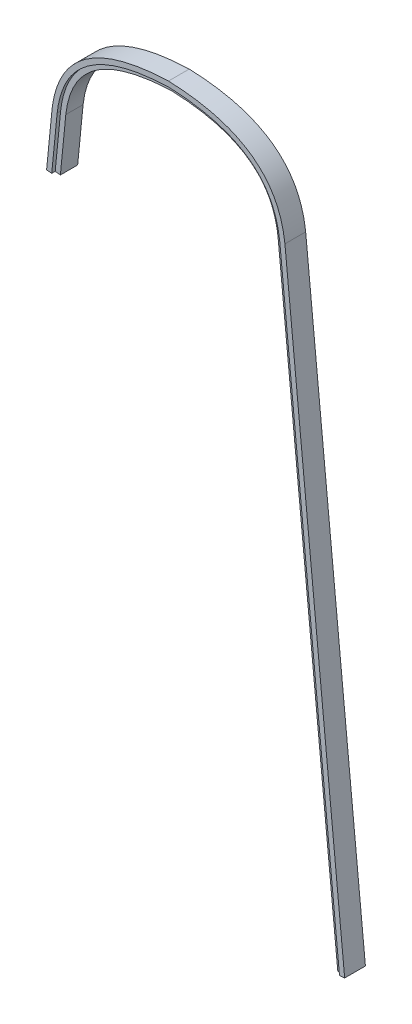
SolidWorks part; units mm, degrees
ref_plane "Front Plane" through (0, 0, 0) normal (0, 0, 1) x (1, 0, 0)
ref_plane "Top Plane" through (0, 0, 0) normal (0, 1, 0) x (1, 0, 0)
ref_plane "Right Plane" through (0, 0, 0) normal (1, 0, 0) x (0, 0, -1)
sketch "Sketch1" plane through (0, 0, 0) normal (0, 0, 1) x (1, 0, 0)
  line L0 (152.2242, 179.7953) -> (97.404, 735.8286)
  line L1 (-102.3813, 685.3442) -> (-97.404, 735.8286)
  line L2 (-111.8604, 686.2788) -> (-102.3813, 685.3442)
  line L3 (152.2242, 179.7953) -> (161.7032, 180.7299)
  line L4 (-166.6875, 130.175) -> (-106.8761, 736.8337) construction
  line L5 (-156.6942, 134.4562) -> (-97.404, 735.8286) construction
  line L6 (-111.8604, 686.2788) -> (-106.8761, 736.8337)
  line L7 (161.7032, 180.7299) -> (106.8761, 736.8337)
  line L8 (0, 0) -> (-166.6875, 130.175) construction
  line L9 (0, 12.0854) -> (-156.6942, 134.4562) construction
  line L10 (0, 0) -> (166.6875, 130.175) construction
  line L11 (0, 12.0854) -> (156.6942, 134.4562) construction
  line L12 (156.6942, 134.4562) -> (97.404, 735.8286) construction
  line L13 (166.6875, 130.175) -> (106.8761, 736.8337) construction
  spline S1 degree 2 poles (-106.8761, 736.8337) (-98.6556, 809.3851) (0, 812.8) knots 0 0 0 1 1 1
  spline S3 degree 2 poles (106.8761, 736.8337) (98.6556, 809.3851) (0, 812.8) knots 0 0 0 1 1 1
  spline S4 degree 1 poles (-97.404, 735.8286) (0, 803.2691) knots 0 0 1 1 construction
  spline S5 degree 1 poles (97.404, 735.8286) (0, 803.2691) knots 0 0 1 1 construction
  spline S8 degree 3 poles (-97.404, 735.8286) (-97.3262, 736.511) (-97.1554, 737.882) (-96.764, 740.5535) (-96.1774, 743.8053) (-95.3214, 747.555) (-93.9799, 752.3593) (-91.9331, 758.0032) (-88.8953, 764.2283) (-85.2743, 769.9432) (-79.6482, 776.9324) (-71.0508, 784.5724) (-60.1295, 790.8325) (-49.8978, 794.9673) (-41.467, 797.6141) (-32.2731, 799.7901) (-23.9758, 801.1984) (-16.9573, 802.076) (-11.5049, 802.6082) (-6.8004, 802.946) (-2.9501, 803.1519) (-0.9798, 803.2339) (0, 803.2691) knots 0.000508 0.000508 0.000508 0.000508 0.016098 0.031688 0.062868 0.094048 0.125228 0.187588 0.249948 0.312308 0.374668 0.499388 0.624108 0.686468 0.748828 0.811188 0.873548 0.904727 0.935907 0.967087 0.982677 0.998267 0.998267 0.998267 0.998267
  spline S9 degree 3 poles (0, 803.2691) (0.9798, 803.2339) (2.9501, 803.1519) (6.8004, 802.946) (11.5049, 802.6082) (16.9573, 802.076) (23.9758, 801.1984) (32.2731, 799.7901) (41.467, 797.6141) (49.8978, 794.9673) (60.1295, 790.8325) (71.0508, 784.5724) (79.6482, 776.9324) (85.2743, 769.9432) (88.8953, 764.2283) (91.9331, 758.0032) (93.9799, 752.3593) (95.3214, 747.555) (96.1774, 743.8053) (96.764, 740.5535) (97.1554, 737.882) (97.3262, 736.511) (97.404, 735.8286) knots 0.000508 0.000508 0.000508 0.000508 0.016098 0.031688 0.062868 0.094048 0.125228 0.187588 0.249948 0.312308 0.374668 0.499388 0.624108 0.686468 0.748828 0.811188 0.873548 0.904727 0.935907 0.967087 0.982677 0.998267 0.998267 0.998267 0.998267
  dimension "D3" = 9.525
  dimension "D4" = 50.8
extrude "Boss-Extrude1" add sketch "Sketch1" along normal blind 19.05
sketch "Sketch2" plane through (0, 0, 19.05) normal (0, 0, 1) x (1, 0, 0)
  line L7 (156.9763, 180.2639) -> (102.1526, 736.3329)
  line L8 (-102.1526, 736.3329) -> (-107.1335, 685.8128)
  line L9 (156.9763, 180.2639) -> (102.1526, 736.3329)
  line L10 (-102.1526, 736.3329) -> (-107.1335, 685.8128)
  spline S0 degree 3 poles (-2519.9949, -2265.8181) (-460.0512, -233.0444) (159.6927, 553.5249) (97.3276, 757.534) (95.3619, 762.1781) (90.5725, 770.7649) (87.749, 774.7087) (81.2153, 781.9433) (77.5041, 785.2346) (69.1465, 791.1813) (64.4995, 793.8362) (54.2358, 798.4953) (48.6194, 800.4989) (-218.966, 873.5222) (-1380.0326, 325.0267) (-3274.732, -1433.6436) knots -4.832472 -4.832472 -4.832472 -4.832472 0.125 0.125 0.25 0.25 0.375 0.375 0.5 0.5 0.625 0.625 0.75 0.75 6.10215 6.10215 6.10215 6.10215 only from (102.1526, 736.3329) to (0, 808.0473)
  spline S1 degree 3 poles (3274.786, -1433.6937) (1380.0547, 325.0163) (218.9685, 873.5229) (-48.6194, 800.4989) (-54.2358, 798.4953) (-64.4995, 793.8362) (-69.1465, 791.1813) (-77.5041, 785.2346) (-81.2153, 781.9433) (-87.749, 774.7087) (-90.5725, 770.7649) (-95.3619, 762.1781) (-97.3276, 757.534) (-159.6926, 553.5254) (460.0483, -233.0408) (2519.9807, -2265.8042) knots -5.102201 -5.102201 -5.102201 -5.102201 0.25 0.25 0.375 0.375 0.5 0.5 0.625 0.625 0.75 0.75 0.875 0.875 5.832461 5.832461 5.832461 5.832461 only from (0, 808.0473) to (-102.1526, 736.3329)
  spline S2 degree 3 poles (102.1526, 736.3329) (101.4964, 742.108) (100.3952, 747.4991) (97.3276, 757.534) (95.3619, 762.1781) (90.5725, 770.7649) (87.749, 774.7087) (81.2153, 781.9433) (77.5041, 785.2346) (69.1465, 791.1813) (64.4995, 793.8362) (54.2358, 798.4953) (48.6194, 800.4989) (30.2988, 805.4986) (16.1223, 807.4792) (0, 808.0473) knots 0 0 0 0 0.125 0.125 0.25 0.25 0.375 0.375 0.5 0.5 0.625 0.625 0.75 0.75 1 1 1 1
  spline S3 degree 3 poles (0, 808.0473) (-16.1223, 807.4792) (-30.2988, 805.4986) (-48.6194, 800.4989) (-54.2358, 798.4953) (-64.4995, 793.8362) (-69.1465, 791.1813) (-77.5041, 785.2346) (-81.2153, 781.9433) (-87.749, 774.7087) (-90.5725, 770.7649) (-95.3619, 762.1781) (-97.3276, 757.534) (-100.3952, 747.4991) (-101.4964, 742.108) (-102.1526, 736.3329) knots 0 0 0 0 0.25 0.25 0.375 0.375 0.5 0.5 0.625 0.625 0.75 0.75 0.875 0.875 1 1 1 1
  dimension "D1" = 4.7498
extrude "Cut-Extrude1" cut sketch "Sketch2" against normal blind 3.175 and the other way through all
